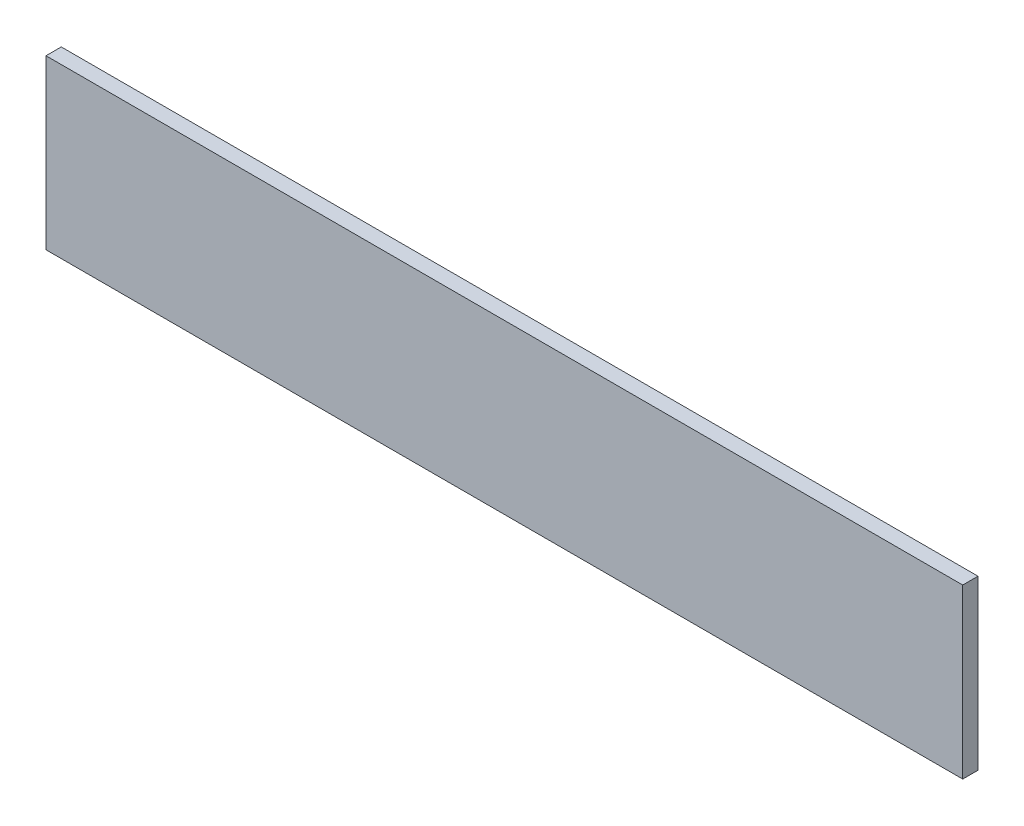
SolidWorks part; units mm, degrees
ref_plane "Plan de face" through (0, 0, 0) normal (0, 0, 1) x (1, 0, 0)
ref_plane "Plan de dessus" through (0, 0, 0) normal (0, 1, 0) x (1, 0, 0)
ref_plane "Plan de droite" through (0, 0, 0) normal (1, 0, 0) x (0, 0, -1)
sketch "Esquisse1" plane through (0, 0, 0) normal (0, 0, 1) x (1, 0, 0)
  line L1 (-600, 0) -> (0, 0)
  line L2 (-600, 0) -> (-600, -110)
  line L3 (-600, -110) -> (0, -110)
  line L4 (0, 0) -> (0, -110)
extrude "Boss.-Extru.1" add sketch "Esquisse1" along normal blind 10
